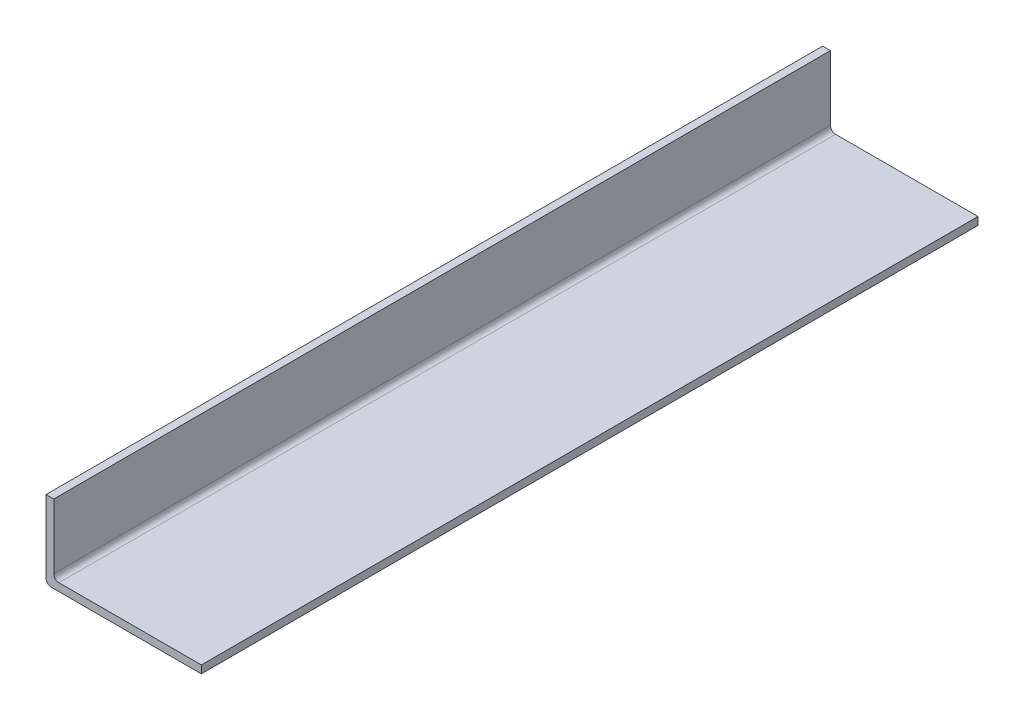
SolidWorks part; units mm, degrees
ref_plane "Front Plane" through (0, 0, 0) normal (0, 0, 1) x (1, 0, 0)
ref_plane "Top Plane" through (0, 0, 0) normal (0, 1, 0) x (1, 0, 0)
ref_plane "Right Plane" through (0, 0, 0) normal (1, 0, 0) x (0, 0, -1)
sketch "Sketch1" plane through (0, 0, 0) normal (0, 0, 1) x (1, 0, 0)
  line L0 (0, 30) -> (0, 0)
  line L1 (0, 0) -> (60, 0)
  line L2 (60, 0) -> (60, 3)
  line L3 (60, 3) -> (3, 3)
  line L4 (3, 3) -> (3, 30)
  line L5 (3, 30) -> (0, 30)
  dimension "D1" = 3
  dimension "D2" = 3
  dimension "D3" = 30
  dimension "D4" = 60
  dimension "D5" = 27
extrude "Boss-Extrude1" add sketch "Sketch1" along normal blind 300
fillet "Fillet1" radius 2 2 edges at (0, 0, 150) (3, 3, 150)
